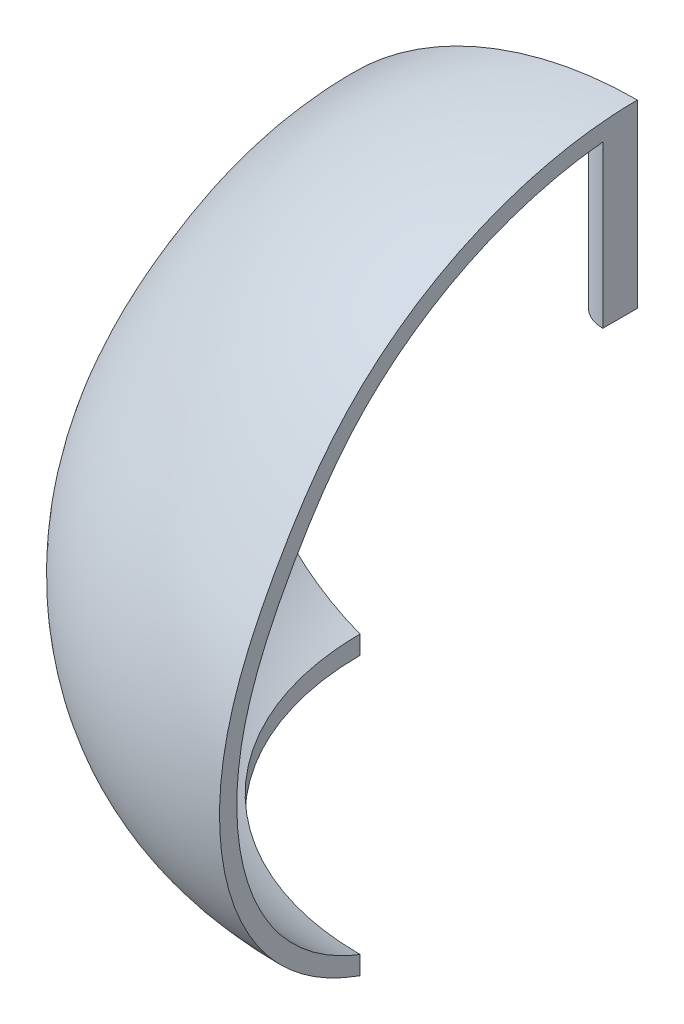
SolidWorks part; units mm, degrees
ref_plane "Front Plane" through (0, 0, 0) normal (0, 0, 1) x (1, 0, 0)
ref_plane "Top Plane" through (0, 0, 0) normal (0, 1, 0) x (1, 0, 0)
ref_plane "Right Plane" through (0, 0, 0) normal (1, 0, 0) x (0, 0, -1)
sketch "Sketch3" plane through (0, 0, 0) normal (0, 0, 1) x (1, 0, 0)
  line L0 (0.0245, 157.0849) -> (0.0245, 152.0849)
  line L1 (0.0245, -20.9434) -> (0.0245, -25.9434)
  line L2 (0.0245, 171.6103) -> (0.0245, -40.6784) construction
  spline S0 degree 3 poles (-103.1746, 0) (-78.8328, -30.0641) (-33.4587, -20.9434) (0.0245, -20.9434) knots 0 0 0 0 1 1 1 1
  spline S1 degree 3 poles (-103.1746, 0) (-114.7602, 14.5762) (-119.8367, 49.2728) (-101.4518, 88.6739) (-71.3798, 134.4794) (-29.75, 152.0849) (0.0245, 152.0849) knots 0 0 0 0 0.250738 0.442513 0.587645 1 1 1 1
  spline S2 degree 1 poles (-107.0747, -3.1288) (0.0245, -25.9434) knots 0 0 1 1 construction
  spline S3 degree 1 poles (-107.0747, -3.1288) (0.0245, 157.0849) knots 0 0 1 1 construction
  spline S4 degree 3 poles (0.0245, -25.9434) (-1.0078, -25.9434) (-3.0527, -25.9607) (-7.3007, -26.054) (-12.7748, -26.2598) (-19.5869, -26.581) (-28.9113, -27.0143) (-40.9004, -27.387) (-55.4438, -26.9753) (-69.7899, -25.0863) (-81.2787, -21.7225) (-89.9598, -17.6028) (-96.1383, -13.7178) (-100.9459, -9.7522) (-104.5344, -6.1303) (-106.2545, -4.1419) (-107.0747, -3.1288) knots -0.000194 -0.000194 -0.000194 -0.000194 0.031062 0.062318 0.12483 0.187342 0.249854 0.374879 0.499903 0.624927 0.749951 0.812464 0.874976 0.937488 0.968744 1 1 1 1
  spline S5 degree 3 poles (-107.0747, -3.1288) (-107.8617, -2.1388) (-109.3756, -0.1005) (-112.0955, 4.1156) (-114.956, 9.6441) (-117.5537, 16.5853) (-119.9627, 26.1346) (-121.1031, 38.4065) (-119.7936, 53.0884) (-116.0899, 67.0475) (-110.6339, 80.233) (-104.0343, 92.719) (-96.8153, 104.7516) (-88.5122, 116.2468) (-78.6677, 126.6978) (-67.4647, 135.7136) (-55.1826, 143.2806) (-42.0542, 149.311) (-28.3211, 153.7314) (-14.2042, 156.4574) (-4.7225, 157.0849) (0.0245, 157.0849) knots -0.000101 -0.000101 -0.000101 -0.000101 0.015525 0.031152 0.062405 0.093658 0.124911 0.187418 0.249924 0.31243 0.374937 0.437443 0.499949 0.562456 0.624962 0.687468 0.749975 0.812481 0.874987 0.937494 1 1 1 1
  dimension "D1" = 5
revolve "Revolve5" add sketch "Sketch3" angle 360 about L2
ref_plane "Plane2" through (0, -30, 0) normal (0, 1, 0) x (1, 0, 0)
sketch "Sketch4" plane through (0, -30, 0) normal (0, 1, 0) x (1, 0, 0)
  circle A0 centre (0, 0) radius 80.1001
extrude "Cut-Extrude2" cut sketch "Sketch4" along normal blind 20
sketch "Sketch5" plane through (0, 0, 0) normal (1, 0, 0) x (0, 0, -1)
  line L0 (-52.4765, 8.1366) -> (52.4765, 8.1366)
  arc A0 (-52.4765, 8.1366) -> (-63.3365, 11.3419) centre (-52.4765, 28.1366) cw
  arc A1 (52.4765, 8.1366) -> (63.3365, 11.3419) centre (52.4765, 28.1366) ccw
  arc A2 (-69.3418, 64.1464) -> (-67.0221, 68.7237) centre (-184.1186, 125.1898) ccw
  arc A3 (70.4941, 63.0471) -> (66.203, 70.3101) centre (188.8284, 137.8602) cw
  arc A4 (78.7462, 39.318) -> (77.2009, 46.2401) centre (214.5664, 73.272) cw
  ellipse E0 centre (0, 56.3684) end of major axis (69.9377, 56.3684) minor radius 43.2422 (66.203, 70.3101) -> (-67.0221, 68.7237) ccw
  ellipse E1 centre (0, 34.6362) end of major axis (79.3292, 34.6362) minor radius 38.6866 (-77.8366, 42.1057) -> (-63.3365, 11.3419) ccw
  ellipse E2 centre (0, 34.6362) end of major axis (79.3292, 34.6362) minor radius 38.6866 (63.3365, 11.3419) -> (78.7462, 39.318) ccw
  spline S0 degree 3 poles (-69.3418, 64.1464) (-73.0617, 57.1522) (-75.8989, 49.7908) (-77.8366, 42.1057) knots 0.114274 0.114274 0.114274 0.114274 1 1 1 1
  spline S1 degree 3 poles (70.4941, 63.0471) (72.3563, 60.1016) (75.0451, 54.6733) (76.6927, 48.8224) (77.2009, 46.2401) knots 0.168182 0.168182 0.168182 0.168182 0.552819 0.845618 0.845618 0.845618 0.845618
  dimension "D1" = 20
  dimension "D2" = 130
  dimension "D3" = 140
  dimension "D4" = 140
extrude "Cut-Extrude3" cut sketch "Sketch5" along normal through all
scale "Scale2" bodies to scale 106 scale about centroid uniform scaling yes scale factor 1
ref_plane "Plane3" through (0, 105, 0) normal (0, 1, 0) x (1, 0, 0)
sketch "Sketch6" plane through (0, 105, 0) normal (0, 1, 0) x (1, 0, 0)
  circle A0 centre (0, 0) radius 10
extrude "Boss-Extrude1" add sketch "Sketch6" against normal up to surface (46.603 mm away)
sketch "Sketch7" plane through (0, 0, 0) normal (0, 0, 1) x (1, 0, 0)
  line L1 (174.4564, -182.2964) -> (-174.4564, -182.2964)
  line L2 (174.4564, -182.2964) -> (174.4564, 182.2964)
  line L3 (174.4564, 182.2964) -> (-174.4564, 182.2964)
  line L4 (-174.4564, -182.2964) -> (-174.4564, 182.2964)
  line L5 (174.4564, -182.2964) -> (-174.4564, 182.2964) construction
  line L6 (174.4564, 182.2964) -> (-174.4564, -182.2964) construction
  point P0 (0, 0)
extrude "Cut-Extrude4" cut sketch "Sketch7" against normal blind 159
ref_plane "Plane4" through (0, 0, 0) normal (1, 0, 0) x (0, 0, -1)
sketch "Sketch8" plane through (0, 0, 0) normal (1, 0, 0) x (0, 0, -1)
  line L1 (163.4096, -166.4472) -> (-163.4096, -166.4472)
  line L2 (163.4096, -166.4472) -> (163.4096, 166.4472)
  line L3 (163.4096, 166.4472) -> (-163.4096, 166.4472)
  line L4 (-163.4096, -166.4472) -> (-163.4096, 166.4472)
  line L5 (163.4096, -166.4472) -> (-163.4096, 166.4472) construction
  line L6 (163.4096, 166.4472) -> (-163.4096, -166.4472) construction
  point P0 (0, 0)
extrude "Cut-Extrude5" cut sketch "Sketch8" along normal blind 200
